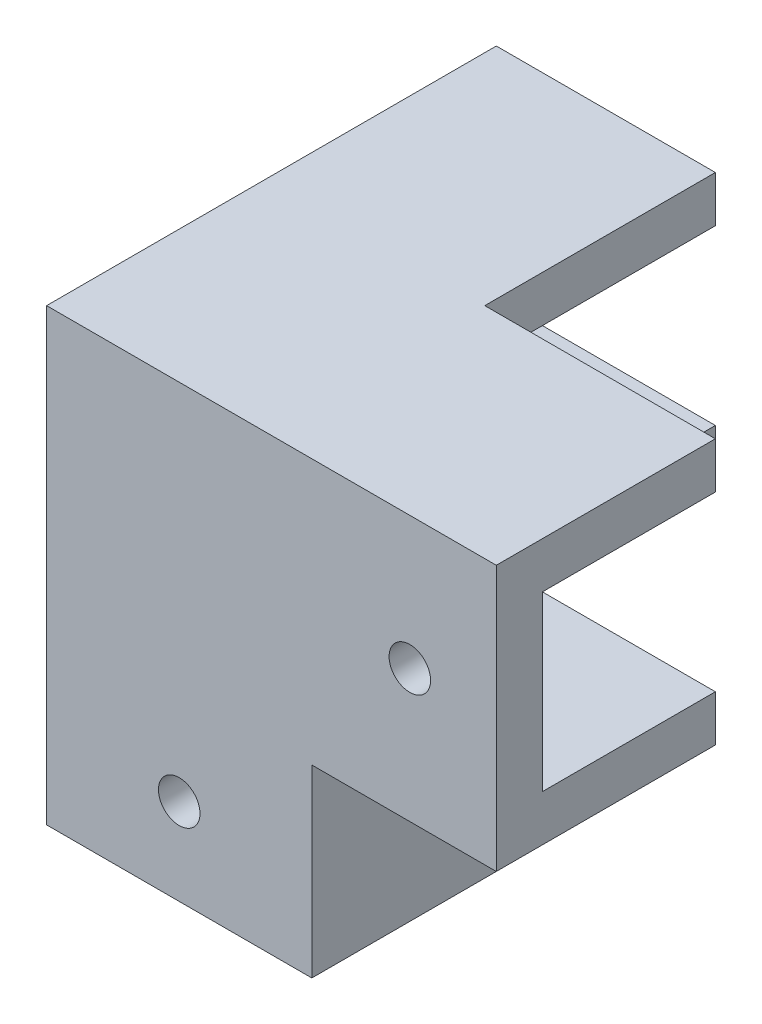
SolidWorks part; units mm, degrees
ref_plane "前视基准面" through (0, 0, 0) normal (0, 0, 1) x (1, 0, 0)
ref_plane "上视基准面" through (0, 0, 0) normal (0, 1, 0) x (1, 0, 0)
ref_plane "右视基准面" through (0, 0, 0) normal (1, 0, 0) x (0, 0, -1)
sketch "草图1" plane through (0, 0, 0) normal (0, 1, 0) x (1, 0, 0)
  line L0 (8.9733, 0.9097) -> (8.9733, -3.0903)
  line L1 (-6.0267, 0.9097) -> (8.9733, 0.9097)
  line L2 (-10.0267, 0.496) -> (-10.0267, -3.0903)
  line L3 (-10.0267, -3.0903) -> (8.9733, -3.0903)
  line L6 (-10.0267, 0.496) -> (-10.0267, 19.9097)
  line L7 (-10.0267, 19.9097) -> (-4.5733, 19.9097)
  line L8 (-6.0267, 0.9097) -> (-6.0267, 15.9097)
  line L13 (-4.5733, 19.9097) -> (8.9733, 19.9097)
  line L15 (-6.0267, 15.9097) -> (8.9733, 15.9097)
  line L16 (8.9733, 19.9097) -> (8.9733, 15.9097)
  dimension "D1" = 4
  dimension "D3" = 4
  dimension "D4" = 15
  dimension "D5" = 15
  dimension "D6" = 4
extrude "凸台-拉伸1" add sketch "草图1" along normal blind 20
sketch "草图2" plane through (8.9733, 0, 0) normal (1, 0, 0) x (0, 0, -1)
  line L1 (-3.0903, 20) -> (15.8097, 20)
  line L2 (-3.0903, 20) -> (-3.0903, 0)
  line L3 (-3.0903, 0) -> (15.8097, 0)
  line L4 (15.8097, 20) -> (15.8097, 0)
  dimension "D1" = 18.9
extrude "凸台-拉伸2" add sketch "草图2" along normal blind 4 separate body
sketch "草图3" plane through (-10.0267, 0, 0) normal (-1, 0, 0) x (0, 0, 1)
  line L1 (3.0903, 20) -> (-0.9097, 20)
  line L2 (3.0903, 20) -> (3.0903, 39)
  line L3 (3.0903, 39) -> (-0.9097, 39)
  line L4 (-0.9097, 20) -> (-0.9097, 39)
  line L5 (-0.9097, 39) -> (-15.9097, 39)
  line L6 (-0.9097, 39) -> (-0.9097, 35)
  line L7 (-0.9097, 35) -> (-15.9097, 35)
  line L8 (-15.9097, 39) -> (-15.9097, 35)
  line M7 (3.0903, 20) -> (-19.9097, 20)
  dimension "D1" = 4
  dimension "D2" = 4
  dimension "D3" = 15
  dimension "D4" = 15
extrude "凸台-拉伸3" add sketch "草图3" against normal blind 39 contours L5 L8 L7 L4 | L4 L2 L3 M7
sketch "草图4" plane through (12.9733, 0, 0) normal (1, 0, 0) x (0, 0, -1)
  line L1 (-3.0903, 20) -> (15.9097, 20)
  line L2 (-3.0903, 20) -> (-3.0903, 16)
  line L3 (-3.0903, 16) -> (15.9097, 16)
  line L4 (15.9097, 20) -> (15.9097, 16)
  dimension "D1" = 4
  dimension "D2" = 19
extrude "凸台-拉伸4" add sketch "草图4" along normal blind 16
sketch "草图5" plane through (0, 0, -15.9097) normal (0, 0, -1) x (-1, 0, 0)
  line L0 (-28.9733, 39) -> (10.0267, 39) construction
  line L1 (10.0267, 35) -> (-8.9733, 35)
  line L2 (10.0267, 35) -> (10.0267, 39)
  line L3 (10.0267, 39) -> (-8.9733, 39)
  line L4 (-8.9733, 35) -> (-8.9733, 39)
  line L6 (10.0267, 35) -> (6.0267, 35)
  line L7 (10.0267, 35) -> (10.0267, 20)
  line L8 (10.0267, 20) -> (6.0267, 20)
  line L9 (6.0267, 35) -> (6.0267, 20)
  line M4 (10.0267, 35) -> (10.0267, 39)
  line M5 (10.0267, 39) -> (-28.9733, 39)
  line M7 (-28.9733, 35) -> (10.0267, 35)
  dimension "D1" = 19
  dimension "D2" = 15
  dimension "D3" = 4
extrude "凸台-拉伸5" add sketch "草图5" along normal blind 20 and the other way blind 15 contours L4 L1 M7 M4 M5 | L1 L9 L8 L7
sketch "草图6" plane through (0, 0, -19.9097) normal (0, 0, -1) x (-1, 0, 0)
  line L0 (-8.9733, 20) -> (-8.9733, 0) construction
  line L1 (10.0267, 20) -> (-8.9733, 20)
  line L2 (10.0267, 20) -> (10.0267, 16)
  line L3 (10.0267, 16) -> (-8.9733, 16)
  line L4 (-8.9733, 20) -> (-8.9733, 16)
  dimension "D1" = 4
extrude "凸台-拉伸6" add sketch "草图6" along normal blind 16
sketch "草图7" plane through (0, 0, 3.0903) normal (0, 0, 1) x (1, 0, 0)
  line L0 (28.9733, 16) -> (28.9733, 39) construction
  line L1 (28.9733, 20) -> (8.9733, 20) construction
  circle A0 centre (21.4733, 27.5) radius 1.8
  dimension "D1" = 3.6
  dimension "D2" = 7.5
  dimension "D3" = 7.5
extrude "切除-拉伸1" cut sketch "草图7" against normal blind 16
sketch "草图8" plane through (-10.0267, 0, 0) normal (-1, 0, 0) x (0, 0, 1)
  line L0 (-35.9097, 16) -> (-35.9097, 39) construction
  line L1 (3.0903, 0) -> (-19.9097, 0) construction
  line L2 (-15.9097, 20) -> (-35.9097, 20) construction
  circle A0 centre (-28.4097, 27.5) radius 1.8
  circle A1 centre (-8.4097, 7.5) radius 1.8
  dimension "D1" = 3.6
  dimension "D2" = 3.6
  dimension "D3" = 7.5
  dimension "D4" = 7.5
  dimension "D5" = 7.5
extrude "切除-拉伸2" cut sketch "草图8" against normal blind 16
sketch "草图9" plane through (0, 0, 3.0903) normal (0, 0, 1) x (1, 0, 0)
  line L0 (-10.0267, 0) -> (12.9733, 0) construction
  circle A0 centre (1.4733, 7.5) radius 1.8
  dimension "D1" = 3.6
  dimension "D2" = 7.5
extrude "切除-拉伸3" cut sketch "草图9" against normal blind 16
